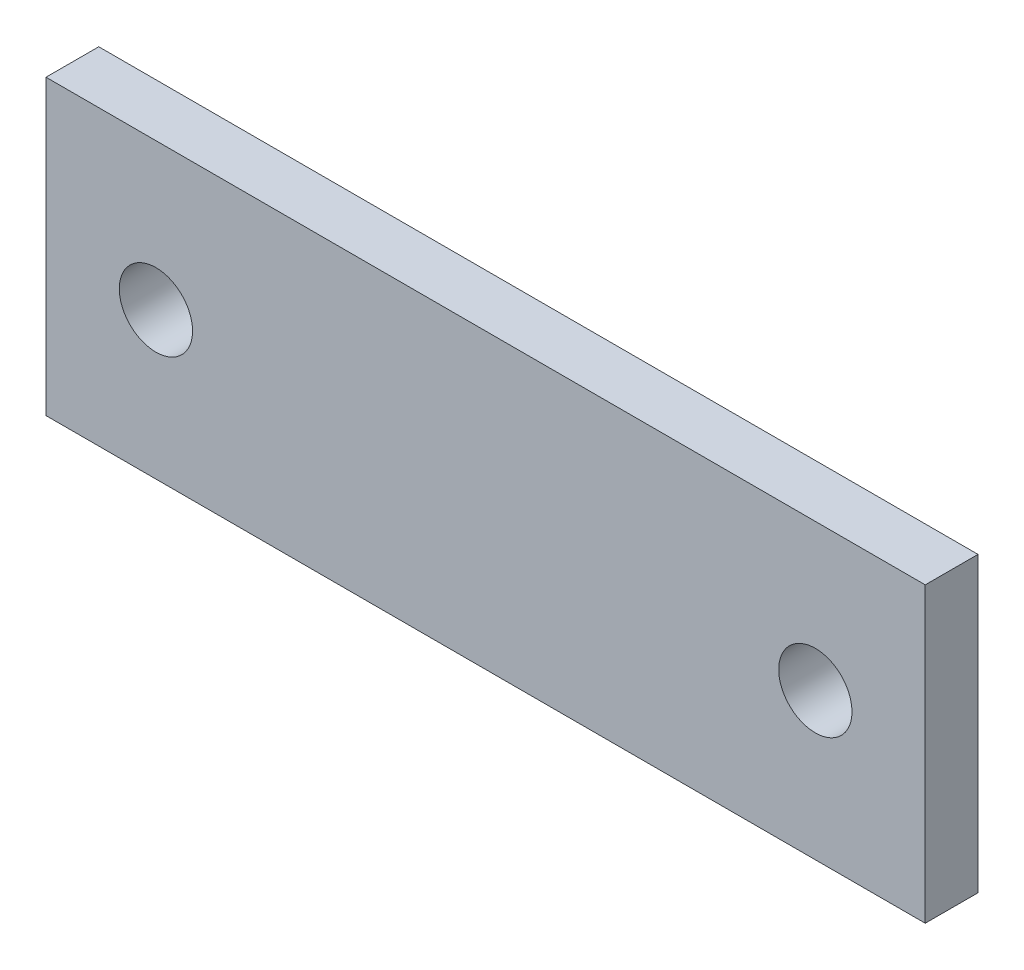
SolidWorks part; units mm, degrees
ref_plane "Front Plane" through (0, 0, 0) normal (0, 0, 1) x (1, 0, 0)
ref_plane "Top Plane" through (0, 0, 0) normal (0, 1, 0) x (1, 0, 0)
ref_plane "Right Plane" through (0, 0, 0) normal (1, 0, 0) x (0, 0, -1)
sketch "Sketch1" plane through (0, 0, 0) normal (0, 0, 1) x (1, 0, 0)
  line L0 (28.575, 0) -> (-28.575, 0) construction
  line L1 (-38.1, -12.7) -> (38.1, -12.7) construction
  line L2 (-38.1, -12.7) -> (-38.1, 12.7) construction
  line L3 (-38.1, 12.7) -> (38.1, 12.7) construction
  line L4 (38.1, -12.7) -> (38.1, 12.7) construction
  line L5 (-38.1, -12.7) -> (38.1, 12.7) construction
  line L6 (-38.1, 12.7) -> (38.1, -12.7) construction
  line L11 (28.575, 0) -> (30.8201, -2.2451) construction
  circle A1 centre (28.575, 0) radius 3.175 construction
  dimension "Hole Size" = 6.35
  dimension "D2" = 45
  dimension "Length (A)" = 76.2
  dimension "Length (C)" = 25.4
  dimension "Hole Spacing" = 57.15
sketch "Sketch2" plane through (0, 0, 0) normal (1, 0, 0) x (0, 0, -1)
  line L0 (-2.286, 12.7) -> (2.286, 12.7)
  dimension "Thickness" = 4.572
sketch "Sketch3" plane through (0, 0, 0) normal (0, 0, 1) x (1, 0, 0)
  line L1 (-38.1, 12.7) -> (38.1, 12.7)
  line L2 (-38.1, 12.7) -> (-38.1, -12.7)
  line L3 (-38.1, -12.7) -> (38.1, -12.7)
  line L4 (38.1, 12.7) -> (38.1, -12.7)
  circle A1 centre (-28.575, 0) radius 3.175
  circle A2 centre (28.575, 0) radius 3.175
  circle A4 centre (28.575, 0) radius 3.175 construction
extrude "Boss-Extrude1" add sketch "Sketch3" along normal up to vertex (2.286 mm away) and the other way up to vertex (2.286 mm away) up to point (0, 12.7, 2.286) other way up to point (0, 12.7, -2.286)
